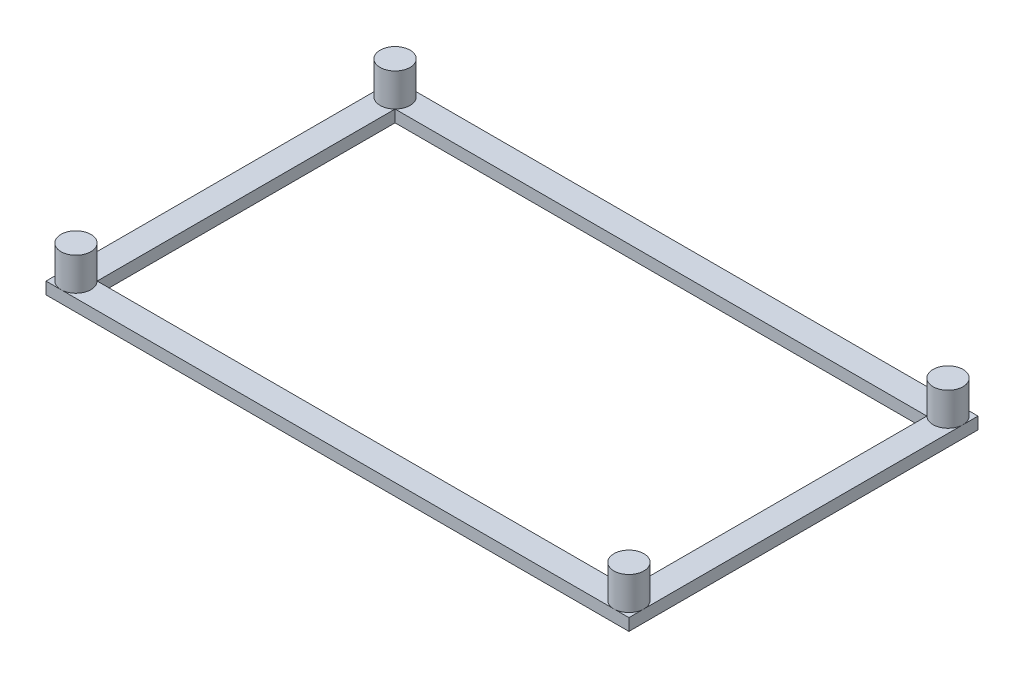
SolidWorks part; units mm, degrees
ref_plane "Front Plane" through (0, 0, 0) normal (0, 0, 1) x (1, 0, 0)
ref_plane "Top Plane" through (0, 0, 0) normal (0, 1, 0) x (1, 0, 0)
ref_plane "Right Plane" through (0, 0, 0) normal (1, 0, 0) x (0, 0, -1)
sketch "Sketch4" plane through (0, 0, 0) normal (0, 1, 0) x (1, 0, 0)
  circle A0 centre (0.3415, 62.6915) radius 1.8415 construction
  circle A1 centre (92.6585, 62.6915) radius 1.8415 construction
  circle A2 centre (92.6585, 115.9685) radius 1.8415 construction
  circle A3 centre (0.3415, 115.9685) radius 1.8415 construction
  circle A4 centre (0.3415, 62.6915) radius 1.8415
  circle A5 centre (92.6585, 62.6915) radius 1.8415
  circle A6 centre (92.6585, 115.9685) radius 1.8415
  circle A7 centre (0.3415, 115.9685) radius 1.8415
  circle A8 centre (0.3415, 115.9685) radius 2.5
  circle A9 centre (0.3415, 62.6915) radius 2.5
  circle A10 centre (92.6585, 62.6915) radius 2.5
  circle A11 centre (92.6585, 115.9685) radius 2.5
  dimension "D1" = 5
extrude "Boss-Extrude4" add sketch "Sketch4" along normal blind 7.5 separate body contours A10 A5 | A5 | A9 A4 | A4 | A8 A7 | A7 | A6 | A11 A6
sketch "Sketch5" plane through (0, 0, 0) normal (0, -1, 0) x (1, 0, 0)
  line L0 (-2.1585, -118.4685) -> (2.1093, -114.2007) construction
  line L1 (-2.1585, -60.1915) -> (95.1585, -60.1915)
  line L2 (-2.1585, -60.1915) -> (-2.1585, -118.4685)
  line L3 (-2.1585, -118.4685) -> (95.1585, -118.4685)
  line L4 (95.1585, -60.1915) -> (95.1585, -118.4685)
  line L5 (2.1093, -64.4593) -> (90.8907, -64.4593)
  line L6 (2.1093, -64.4593) -> (2.1093, -114.2007)
  line L7 (2.1093, -114.2007) -> (90.8907, -114.2007)
  line L8 (90.8907, -64.4593) -> (90.8907, -114.2007)
  line L9 (0.3415, -115.9685) -> (2.1093, -114.2007) construction
  circle A0 centre (92.6585, -115.9685) radius 2.5 construction
  circle A1 centre (0.3415, -62.6915) radius 2.5 construction
  circle A2 centre (0.3415, -115.9685) radius 2.5 construction
  circle A3 centre (92.6585, -62.6915) radius 2.5 construction
extrude "Boss-Extrude5" add sketch "Sketch5" against normal blind 2
